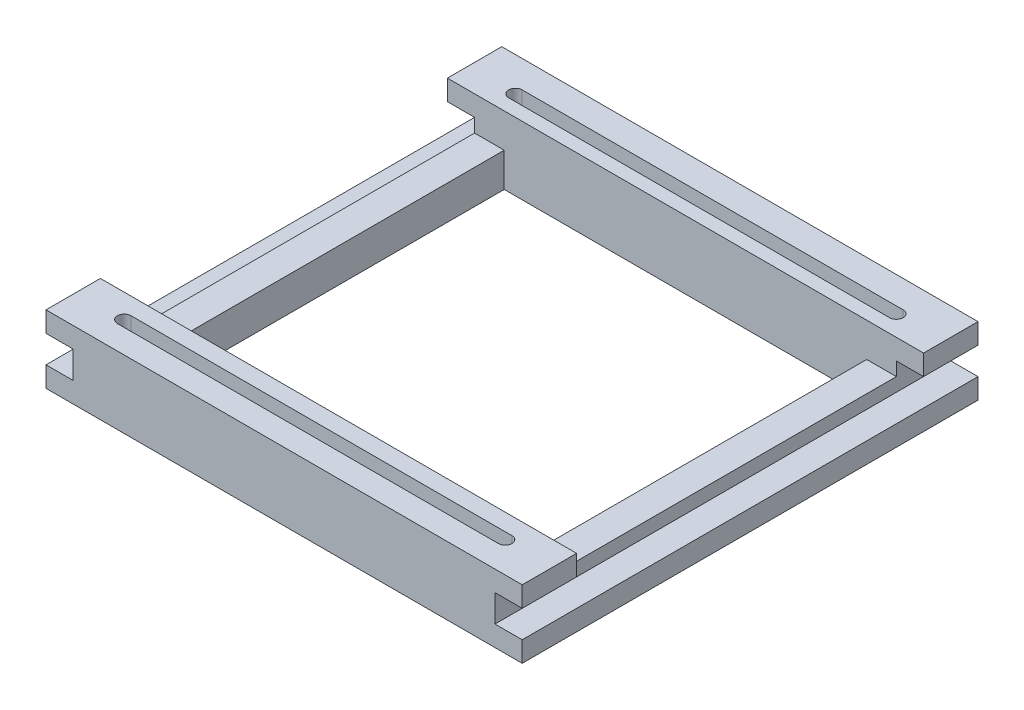
SolidWorks part; units mm, degrees
ref_plane "Plan de face" through (0, 0, 0) normal (0, 0, 1) x (1, 0, 0)
ref_plane "Plan de dessus" through (0, 0, 0) normal (0, 1, 0) x (1, 0, 0)
ref_plane "Plan de droite" through (0, 0, 0) normal (1, 0, 0) x (0, 0, -1)
sketch "Esquisse1" plane through (0, 0, 0) normal (0, 1, 0) x (1, 0, 0)
  line L0 (26.6418, 25.5) -> (-26.6418, 25.5)
  line L1 (-35, -33.5) -> (35, -33.5)
  line L2 (-35, -33.5) -> (-35, 33.5)
  line L3 (-35, 33.5) -> (35, 33.5)
  line L4 (35, -33.5) -> (35, 33.5)
  line L5 (-35, -33.5) -> (35, 33.5) construction
  line L6 (-35, 33.5) -> (35, -33.5) construction
  line L7 (-26.6418, 25.5) -> (-26.6418, -25.5)
  line L8 (-26.6418, -25.5) -> (26.6418, -25.5)
  line L9 (26.6418, -25.5) -> (26.6418, 25.5)
  point P0 (0, 0)
  dimension "D1" = 70
  dimension "D2" = 67
  dimension "D3" = 8
extrude "Boss.-Extru.1" add sketch "Esquisse1" along normal blind 10
sketch "Esquisse2" plane through (0, 10, 0) normal (0, 1, 0) x (1, 0, 0)
  line L0 (-35, 33.5) -> (-35, -33.5) construction
  line L1 (-26.6418, 25.5) -> (-35, 25.5)
  line L2 (-26.6418, 25.5) -> (-26.6418, -25.5)
  line L3 (-26.6418, -25.5) -> (-35, -25.5)
  line L4 (-35, 25.5) -> (-35, -25.5)
  line L5 (35, -33.5) -> (35, 33.5) construction
  line L6 (26.6418, 25.5) -> (35, 25.5)
  line L7 (26.6418, 25.5) -> (26.6418, -25.5)
  line L8 (26.6418, -25.5) -> (35, -25.5)
  line L9 (35, 25.5) -> (35, -25.5)
  line L10 (-26.6418, -25.5) -> (26.6418, -25.5) construction
extrude "Enlèv. mat.-Extru.1" cut sketch "Esquisse2" against normal blind 5
sketch "Esquisse3" plane through (0, 0, 33.5) normal (0, 0, 1) x (1, 0, 0)
  line L0 (35, 10) -> (35, 0) construction
  line L1 (35, 3) -> (31, 3)
  line L2 (35, 3) -> (35, 7)
  line L3 (35, 7) -> (31, 7)
  line L4 (31, 3) -> (31, 7)
  line L5 (-35, 10) -> (-35, 0) construction
  line L6 (-35, 7) -> (-31, 7)
  line L7 (-35, 7) -> (-35, 3)
  line L8 (-35, 3) -> (-31, 3)
  line L9 (-31, 7) -> (-31, 3)
  line L10 (-35, 0) -> (35, 0) construction
  point P12 (-35, 5)
  dimension "D1" = 4
  dimension "D2" = 4
  dimension "D3" = 5
  dimension "D4" = 4
extrude "Enlèv. mat.-Extru.2" cut sketch "Esquisse3" against normal through all
sketch "Esquisse4" plane through (0, 10, 0) normal (0, 1, 0) x (1, 0, 0)
  line L0 (-28, 29.5) -> (28, 29.5)
  line L1 (28, 27.5) -> (-28, 27.5)
  line L2 (35, 33.5) -> (-35, 33.5) construction
  line L3 (-35, 33.5) -> (-35, 25.5) construction
  line L4 (35, 25.5) -> (35, 33.5) construction
  line L5 (28, -30) -> (-28, -30)
  line L6 (-28, -28) -> (28, -28)
  line L7 (-35, -33.5) -> (35, -33.5) construction
  line L8 (-35, -25.5) -> (-35, -33.5) construction
  line L9 (35, -33.5) -> (35, -25.5) construction
  arc A0 (-28, 29.5) -> (-28, 27.5) centre (-28, 28.5) ccw
  arc A1 (28, 27.5) -> (28, 29.5) centre (28, 28.5) ccw
  arc A2 (28, -30) -> (28, -28) centre (28, -29) ccw
  arc A3 (-28, -28) -> (-28, -30) centre (-28, -29) ccw
  dimension "D1" = 2
  dimension "D2" = 2
  dimension "D3" = 5
  dimension "D4" = 5
  dimension "D5" = 7
  dimension "D6" = 7
  dimension "D7" = 4.5
  dimension "D8" = 4.5
  dimension "D9" = 7
  dimension "D10" = 7
extrude "Enlèv. mat.-Extru.3" cut sketch "Esquisse4" against normal blind 5 contours L0 A1 L1 A0 | L5 A3 L6 A2
